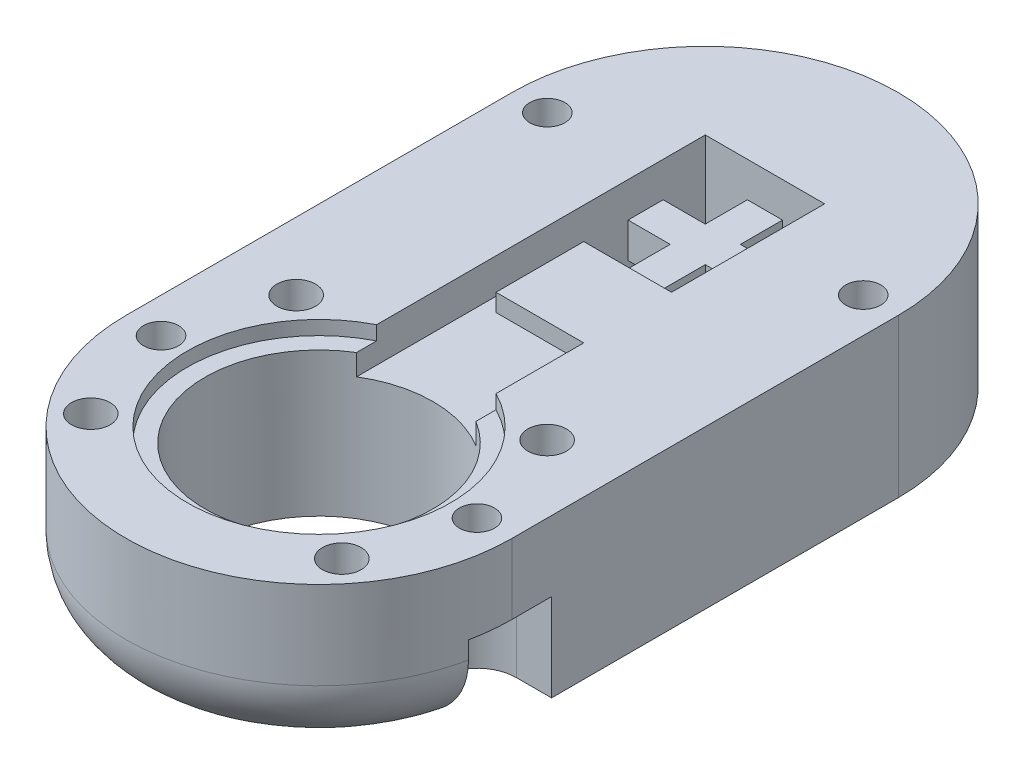
SolidWorks part; units mm, degrees
ref_plane "Front Plane" through (0, 0, 0) normal (0, 0, 1) x (1, 0, 0)
ref_plane "Top Plane" through (0, 0, 0) normal (0, 1, 0) x (1, 0, 0)
ref_plane "Right Plane" through (0, 0, 0) normal (1, 0, 0) x (0, 0, -1)
sketch "Sketch1" plane through (0, 0, 0) normal (0, 1, 0) x (1, 0, 0)
  line L0 (-11, 0) -> (-11, 22.01)
  line L1 (-0.01, 33) -> (0.01, 33)
  line L2 (11, 22.01) -> (11, 0)
  circle A1 centre (0, 0) radius 11 construction
  circle A2 centre (0, 0) radius 6.5
  arc A3 (-11, 0) -> (11, 0) centre (0, 0) ccw
  arc A4 (11, 22.01) -> (0.01, 33) centre (0.01, 22.01) ccw
  arc A5 (-11, 22.01) -> (-0.01, 33) centre (-0.01, 22.01) cw
  dimension "D1" = 13
  dimension "D2" = 22
  dimension "D4" = 10.99
  dimension "D3" = 33
extrude "Boss-Extrude1" add sketch "Sketch1" along normal blind 9
sketch "Sketch2" plane through (0, 9, 0) normal (0, 1, 0) x (1, 0, 0)
  line L0 (-11, 0) -> (11, 0) construction
  line L2 (0, 6.5) -> (0, 0) construction
  circle A1 centre (-7.15, 5.85) radius 1.1
  circle A2 centre (-7.15, -5.85) radius 1.1
  circle A5 centre (0, 0) radius 6.5 construction
  circle A6 centre (7.15, -5.85) radius 1.1
  circle A7 centre (7.15, 5.85) radius 1.1
  arc A8 (-11, 0) -> (11, 0) centre (0, 0) ccw construction
  dimension "D1" = 2.2
  dimension "D2" = 7.15
  dimension "D3" = 5.85
extrude "Cut-Extrude1" cut sketch "Sketch2" against normal blind 3
sketch "Sketch3" plane through (0, 9, 0) normal (0, 1, 0) x (1, 0, 0)
  line L0 (-11, 0) -> (11, 0) construction
  line L2 (0, 6.5) -> (0, 0) construction
  circle A0 centre (-9, 0) radius 1
  circle A1 centre (9, 0) radius 1
  dimension "D1" = 2
  dimension "D4" = 2
  dimension "D2" = 9
  dimension "D3" = 9
extrude "Cut-Extrude2" cut sketch "Sketch3" against normal blind 20 contours A0
sketch "Sketch4" plane through (0, 0, 0) normal (0, -1, 0) x (1, 0, 0)
  line L0 (-9, 2.25) -> (-10.7674, 2.25)
  line L1 (-9, -2.25) -> (-11, -2.25)
  line L2 (-11, -2.25) -> (-12, 0)
  line L3 (-12, 0) -> (-10.7674, 2.25)
  line L4 (-11, 0) -> (11, 0) construction
  line L6 (0, 6.5) -> (0, 0) construction
  line L11 (-11, -22.01) -> (-11, 0) construction
  line L12 (12, 0) -> (10.7674, 2.25)
  line L13 (11, -2.25) -> (12, 0)
  line L14 (9, -2.25) -> (11, -2.25)
  line L15 (9, 2.25) -> (10.7674, 2.25)
  circle A0 centre (-9, 0) radius 2.25 construction
  arc A3 (-9, 2.25) -> (-9, -2.25) centre (-9, 0) cw
  arc A5 (11, 0) -> (-11, 0) centre (0, 0) ccw construction
  arc A6 (9, 2.25) -> (9, -2.25) centre (9, 0) ccw
  circle A7 centre (0, 0) radius 6.5 construction
  dimension "D1" = 4.5
  dimension "D2" = 1
extrude "Cut-Extrude3" cut sketch "Sketch4" against normal blind 5 contours L0 L3 L2 L1 A3
sketch "Sketch6" plane through (0, 0, 0) normal (0, -1, 0) x (1, 0, 0)
  line L0 (0, -6.5) -> (0, -33) construction
  line L1 (0.01, -33) -> (-0.01, -33) construction
  line L3 (-11, -22.01) -> (11, -22.01) construction
  line L4 (-3.4, -25.41) -> (3.4, -25.41)
  line L5 (-3.4, -25.41) -> (-3.4, -18.61)
  line L6 (-3.4, -18.61) -> (3.4, -18.61)
  line L7 (3.4, -25.41) -> (3.4, -18.61)
  line L8 (-3.4, -25.41) -> (3.4, -18.61) construction
  line L9 (-3.4, -18.61) -> (3.4, -25.41) construction
  point P5 (0, -22.01)
  dimension "D1" = 6.8
  dimension "D2" = 6.8
extrude "Cut-Extrude4" cut sketch "Sketch6" against normal blind 5
sketch "Sketch7" plane through (0, 5, 0) normal (0, -1, 0) x (1, 0, 0)
  line L0 (0, -18.61) -> (0, -25.41) construction
  line L1 (3.4, -18.61) -> (-3.4, -18.61) construction
  line L2 (-3.4, -25.41) -> (3.4, -25.41) construction
  line L3 (-3.4, -22.01) -> (3.4, -22.01) construction
  line L4 (-3.4, -18.61) -> (-3.4, -25.41) construction
  line L5 (3.4, -25.41) -> (3.4, -18.61) construction
  line L6 (3.4, -18.61) -> (1, -18.61)
  line L7 (-3.4, -18.61) -> (-1, -18.61)
  line L8 (-3.4, -18.61) -> (-3.4, -21.01)
  line L9 (-3.4, -21.01) -> (-1, -21.01)
  line L10 (-1, -18.61) -> (-1, -21.01)
  line L11 (3.4, -18.61) -> (3.4, -21.01)
  line L12 (3.4, -21.01) -> (1, -21.01)
  line L13 (1, -18.61) -> (1, -21.01)
  line L14 (3.4, -25.41) -> (1, -25.41)
  line L15 (3.4, -25.41) -> (3.4, -23.01)
  line L16 (3.4, -23.01) -> (1, -23.01)
  line L17 (1, -25.41) -> (1, -23.01)
  line L18 (-3.4, -25.41) -> (-1, -25.41)
  line L19 (-3.4, -25.41) -> (-3.4, -23.01)
  line L20 (-3.4, -23.01) -> (-1, -23.01)
  line L21 (-1, -25.41) -> (-1, -23.01)
  dimension "D1" = 1
  dimension "D2" = 1
extrude "Cut-Extrude5" cut sketch "Sketch7" against normal blind 5
fillet "Fillet2" radius 4 1 edges at (0, 0, 11)
sketch "Sketch8" plane through (0, 0, 0) normal (0, -1, 0) x (1, 0, 0)
  line L0 (-11, -22.01) -> (11, -22.01) construction
  line L1 (-9, 0) -> (-9, -22.01) construction
  line L2 (0, -18.61) -> (0, -25.41) construction
  line L3 (3.4, -18.61) -> (-3.4, -18.61) construction
  line L4 (-1, -25.41) -> (1, -25.41) construction
  circle A0 centre (-9, -22.01) radius 1
  circle A1 centre (9, -22.01) radius 1
  dimension "D1" = 2
extrude "Cut-Extrude6" cut sketch "Sketch8" against normal blind 20
sketch "Sketch9" plane through (0, 9, 0) normal (0, 1, 0) x (1, 0, 0)
  circle A0 centre (0, 0) radius 7.5
  circle A1 centre (0, 0) radius 6.5 construction
  dimension "D1" = 1
extrude "Cut-Extrude7" cut sketch "Sketch9" against normal blind 0.8
sketch "Sketch10" plane through (0, 9, 0) normal (0, 1, 0) x (1, 0, 0)
  line L0 (3.4, 23.01) -> (3.4, 25.41) construction
  line L1 (-3.4, 25.41) -> (3.4, 25.41)
  line L2 (-3.4, 25.41) -> (-3.4, 5.5399)
  line L3 (-3.4, 5.5399) -> (3.4, 5.5399)
  line L4 (3.4, 25.41) -> (3.4, 5.5399)
  circle A0 centre (0, 0) radius 6.5 construction
  point P7 (0, 0)
extrude "Cut-Extrude8" cut sketch "Sketch10" against normal blind 2
sketch "Sketch11" plane through (3.4, 0, 0) normal (-1, 0, 0) x (0, 0, 1)
  line L0 (-6.6851, 9) -> (-25.41, 9) construction
  line L5 (-16.6851, 9) -> (-11.6851, 9)
  line L6 (-16.6851, 9) -> (-16.6851, 8)
  line L7 (-16.6851, 8) -> (-11.6851, 8)
  line L8 (-11.6851, 9) -> (-11.6851, 8)
  line L9 (-6.6851, 9) -> (-6.6851, 8.2) construction
  dimension "D1" = 5
  dimension "D2" = 1
  dimension "D3" = 5
extrude "Boss-Extrude2" add sketch "Sketch11" along normal blind 5
